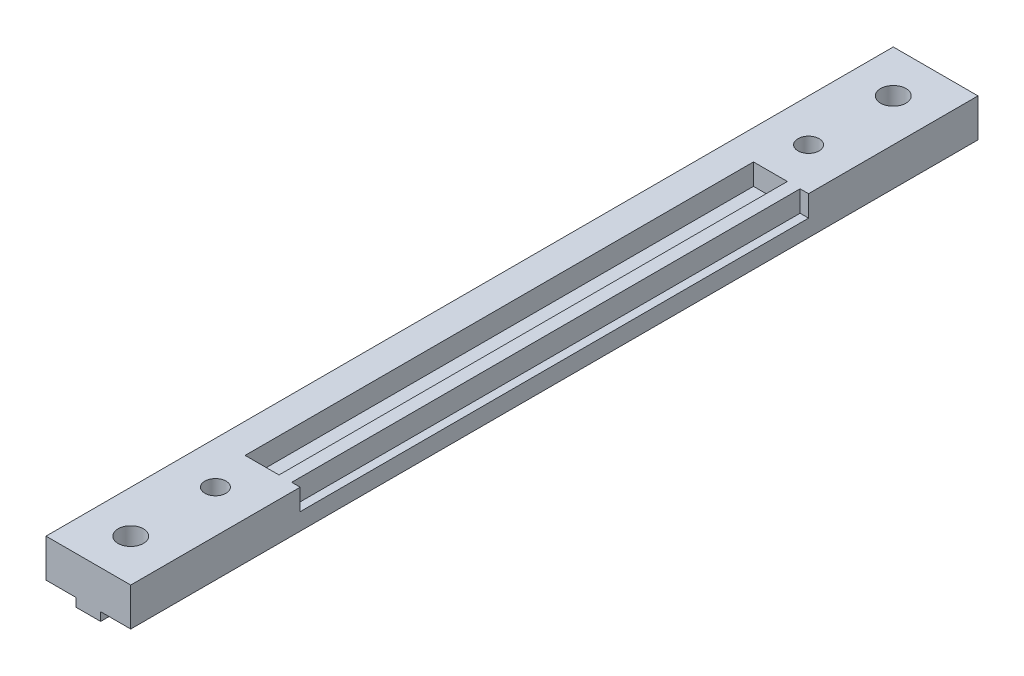
SolidWorks part; units mm, degrees
ref_plane "Front Plane" through (0, 0, 0) normal (0, 0, 1) x (1, 0, 0)
ref_plane "Top Plane" through (0, 0, 0) normal (0, 1, 0) x (1, 0, 0)
ref_plane "Right Plane" through (0, 0, 0) normal (1, 0, 0) x (0, 0, -1)
sketch "Sketch1" plane through (0, 0, 0) normal (0, 0, 1) x (1, 0, 0)
  line L0 (-5, 0) -> (5, 0)
  line L1 (5, 0) -> (5, -4.5)
  line L2 (5, -4.5) -> (1.45, -4.5)
  line L3 (1.45, -4.5) -> (1.45, -5.5)
  line L4 (1.45, -5.5) -> (-1.45, -5.5)
  line L5 (-1.45, -5.5) -> (-1.45, -4.5)
  line L6 (-1.45, -4.5) -> (-5, -4.5)
  line L7 (-5, -4.5) -> (-5, 0)
  point P9 (0, 0)
  dimension "D1" = 10
  dimension "D2" = 4.5
  dimension "D3" = 1
  dimension "D4" = 2.9
extrude "Main" add sketch "Sketch1" along normal blind 100
sketch "Sketch2" plane through (0, 0, 0) normal (0, 1, 0) x (1, 0, 0)
  line L0 (5, -100) -> (-5, -100) construction
  line L1 (5, 0) -> (-5, 0) construction
  circle A0 centre (0, -85) radius 1.25
  circle A1 centre (0, -15) radius 1.25
  circle A2 centre (0, -5) radius 1.5
  circle A3 centre (0, -95) radius 1.5
  dimension "D1" = 2.5
  dimension "D4" = 3
  dimension "D2" = 15
  dimension "D3" = 70
  dimension "D5" = 5
  dimension "D6" = 5
extrude "MainHoles" cut sketch "Sketch2" against normal through all
sketch "Sketch3" plane through (0, 0, 0) normal (0, 1, 0) x (1, 0, 0)
  line L1 (5, -100) -> (5, 0) construction
  line L3 (5, -20) -> (4, -20)
  line L4 (5, -20) -> (5, -80)
  line L6 (-1.5, -20) -> (2.5, -20)
  line L7 (-1.5, -20) -> (-1.5, -80)
  line L8 (-1.5, -80) -> (2.5, -80)
  line L9 (2.5, -20) -> (2.5, -80)
  line L10 (5, -100) -> (-5, -100) construction
  line L11 (5, -80) -> (4, -80)
  line L12 (4, -20) -> (4, -80)
  point P10 (-1.5, -18.1876)
  point P11 (5, -80.0195)
  dimension "D1" = 4
  dimension "D2" = 20
  dimension "D3" = 20
  dimension "D4" = 2.5
  dimension "D5" = 1
extrude "PinHoles" cut sketch "Sketch3" against normal blind 2.5
